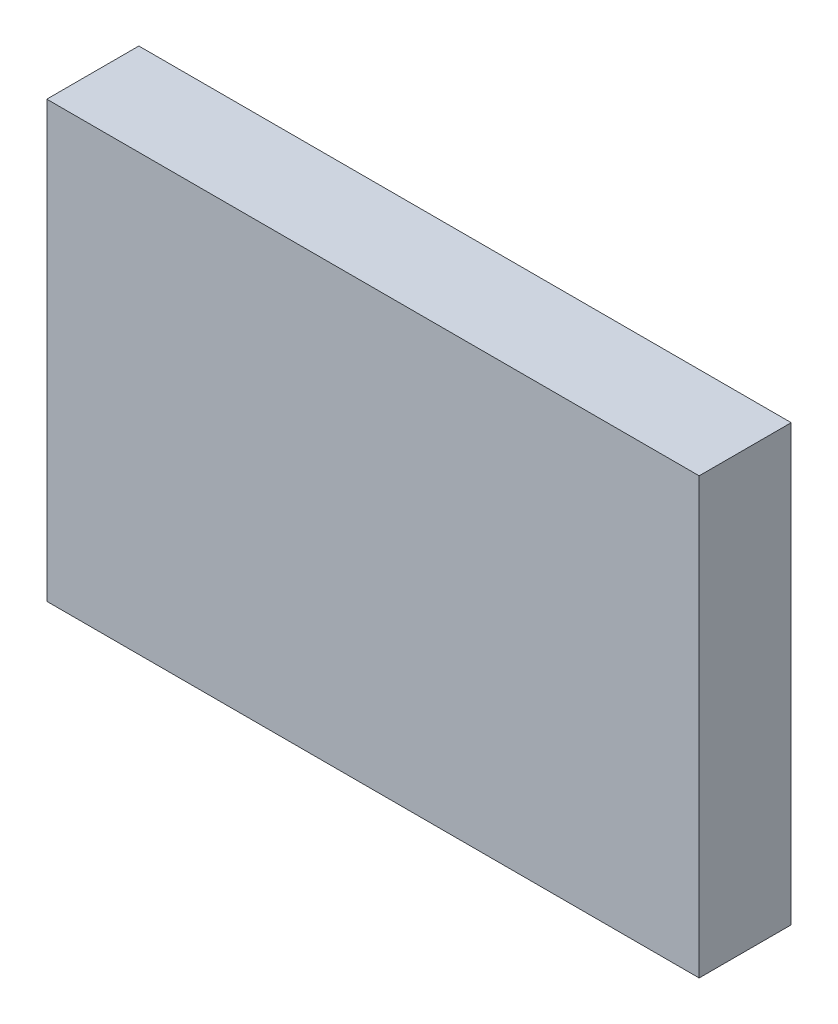
SolidWorks part; units mm, degrees
material "Balsa"
ref_plane "Front Plane" through (0, 0, 0) normal (0, 0, 1) x (1, 0, 0)
ref_plane "Top Plane" through (0, 0, 0) normal (0, 1, 0) x (1, 0, 0)
ref_plane "Right Plane" through (0, 0, 0) normal (1, 0, 0) x (0, 0, -1)
sketch "Sketch1" plane through (0, 0, 0) normal (0, 0, 1) x (1, 0, 0)
  line L1 (0, 0) -> (45, 0)
  line L2 (0, 0) -> (0, 30)
  line L3 (0, 30) -> (45, 30)
  line L4 (45, 0) -> (45, 30)
  dimension "D1" = 45
  dimension "D2" = 30
extrude "Boss-Extrude1" add sketch "Sketch1" along normal blind 6.35
